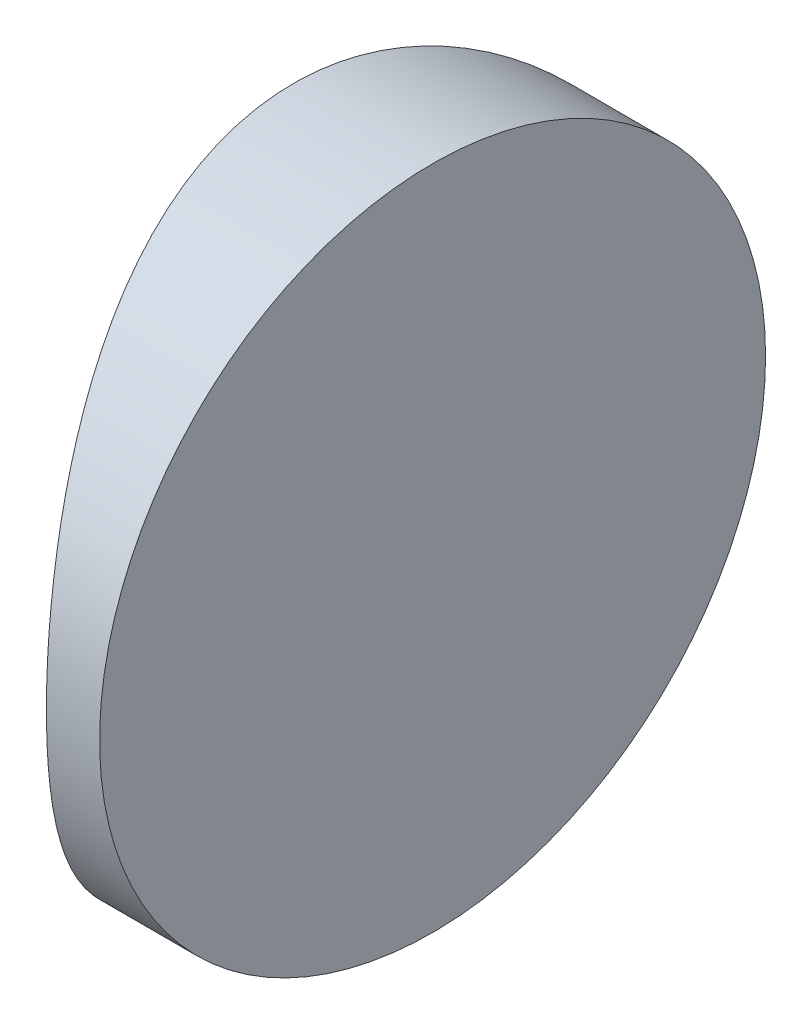
SolidWorks part; units mm, degrees
ref_plane "前视基准面" through (0, 0, 0) normal (0, 0, 1) x (1, 0, 0)
ref_plane "上视基准面" through (0, 0, 0) normal (0, 1, 0) x (1, 0, 0)
ref_plane "右视基准面" through (0, 0, 0) normal (1, 0, 0) x (0, 0, -1)
sketch "草图1" plane through (0, 0, 0) normal (0, 1, 0) x (1, 0, 0)
  line L0 (10.7432, 0) -> (-55.502, 0) construction
  line L1 (-18.2716, 12.5) -> (-16.2748, 12.5)
  line L2 (-18.2716, -12.5) -> (-16.2748, -12.5)
  line L3 (-16.2748, 12.5) -> (-16.2748, -12.5)
  arc A0 (-18.2716, 12.5) -> (-18.2716, -12.5) centre (4.3552, 0) ccw
  point P19 (-21.4948, 0)
  point P20 (-16.2748, 0)
  dimension "D2" = 12.5
  dimension "D3" = 25.85
  dimension "D4" = 5.22
  dimension "D1" = 12.5
extrude "凸台-拉伸1" add sketch "草图1" along normal blind 25 contours A0 L2 L3 L1
sketch "草图2" plane through (-16.2748, 0, 0) normal (1, 0, 0) x (0, 0, -1)
  line L0 (12.5, 0) -> (-12.5, 0) construction
  line L7 (-12.5, 0) -> (12.5, 0)
  line L8 (12.5, 0) -> (12.5, 25)
  line L9 (12.5, 25) -> (-12.5, 25)
  line L10 (-12.5, 25) -> (-12.5, 0)
  line L11 (-12.5, 0) -> (12.5, 0)
  line L12 (12.5, 0) -> (12.5, 25)
  line L13 (12.5, 25) -> (-12.5, 25)
  line L14 (-12.5, 25) -> (-12.5, 0)
  circle A0 centre (0, 12.5) radius 12.5
  line M1 (-12.5, 0) -> (12.5, 0)
  line M2 (12.5, 0) -> (12.5, 25)
  line M3 (12.5, 25) -> (-12.5, 25)
  line M4 (-12.5, 25) -> (-12.5, 0)
  dimension "D1" = 25
  dimension "D4" = 12.5
  dimension "D2" = 12.5
  dimension "D3" = 0
extrude "切除-拉伸8" cut sketch "草图2" against normal blind 12.7 contours A0 L13 M4 | A0 L12 M3 | A0 L11 M2 | A0 L14 M1
